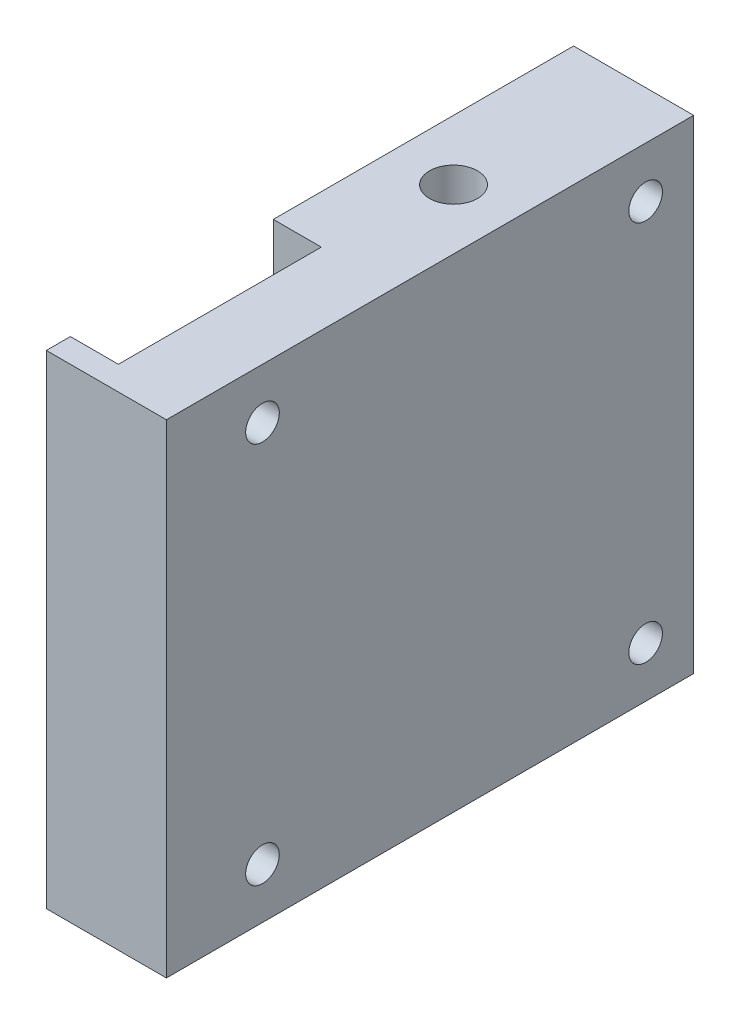
SolidWorks part; units mm, degrees
ref_plane "Front Plane" through (0, 0, 0) normal (0, 0, 1) x (1, 0, 0)
ref_plane "Top Plane" through (0, 0, 0) normal (0, 1, 0) x (1, 0, 0)
ref_plane "Right Plane" through (0, 0, 0) normal (1, 0, 0) x (0, 0, -1)
sketch "Sketch2" plane through (34.4736, 0, 0) normal (-1, 0, 0) x (0, 0, 1)
  line L0 (280.9388, 336.0766) -> (282.5512, 320.4454) construction
  line L1 (301.6995, 347.1848) -> (301.6995, 307.6848) construction
  line L2 (261.7905, 348.3924) -> (301.6995, 348.3924)
  line L3 (261.7905, 348.3924) -> (261.7905, 308.1295)
  line L4 (261.7905, 308.1295) -> (301.6995, 308.1295)
  line L5 (301.6995, 348.3924) -> (301.6995, 308.1295)
  line L6 (261.7905, 348.3924) -> (301.6995, 308.1295) construction
  line L7 (261.7905, 308.1295) -> (301.6995, 348.3924) construction
  line L8 (295.1, 308.1295) -> (299.7929, 308.1295) construction
  line L9 (297.6995, 345.5848) -> (297.6995, 342.7848) construction
  line L10 (261.7905, 328.261) -> (301.6995, 328.261) construction
  line L11 (281.745, 348.3924) -> (281.745, 308.1295) construction
  circle A0 centre (281.765, 328.1193) radius 8 construction
  circle A2 centre (297.6995, 344.1848) radius 1.4 construction
  circle A3 centre (297.6995, 344.1848) radius 1.4
  circle A4 centre (297.6995, 312.3371) radius 1.4
  circle A5 centre (265.7905, 312.3371) radius 1.4
  circle A6 centre (265.7905, 344.1848) radius 1.4
  point P4 (281.745, 328.261)
  point P5 (281.745, 328.261)
  point P19 (297.6995, 344.1848)
  point P24 (281.745, 348.3924)
  dimension "D2" = 2.8
  dimension "D1" = 40.2629
extrude "Boss-Extrude1" add sketch "Sketch2" along normal blind 10
sketch "Sketch5" plane through (24.4736, 0, 0) normal (-1, 0, 0) x (0, 0, 1)
  line L0 (297.6995, 344.6649) -> (297.6995, 343.4848) construction
  line L1 (264.4344, 311.9894) -> (267.1466, 312.6848) construction
  line L2 (265.0495, 312.6848) -> (275.5245, 312.6848) construction
  line L3 (264.3905, 344.1848) -> (267.1905, 344.1848) construction
  circle A0 centre (297.6995, 344.0749) radius 3
  circle A2 centre (265.7905, 312.3371) radius 1.4 construction
  circle A3 centre (265.7905, 312.3371) radius 3
  circle A4 centre (297.6995, 312.3371) radius 3
  circle A5 centre (265.7905, 344.1848) radius 1.4 construction
  circle A6 centre (265.7905, 344.1848) radius 3
  dimension "D1" = 6
  dimension "D2" = 6
  dimension "D3" = 6
  dimension "D4" = 6
extrude "Cut-Extrude1" cut sketch "Sketch5" against normal blind 4
sketch "Sketch6" plane through (24.4736, 0, 0) normal (-1, 0, 0) x (0, 0, 1)
  line L2 (301.6995, 348.3924) -> (261.7905, 348.3924) construction
  line L7 (286.7995, 348.3924) -> (301.6995, 348.3924)
  line L8 (286.7995, 348.3924) -> (286.7995, 318.3924)
  line L9 (286.7995, 318.3924) -> (301.6995, 318.3924)
  line L10 (301.6995, 348.3924) -> (301.6995, 318.3924)
  line L11 (286.7995, 348.3924) -> (301.6995, 318.3924) construction
  line L12 (286.7995, 318.3924) -> (301.6995, 348.3924) construction
  line L13 (301.6995, 308.1295) -> (301.6995, 348.3924) construction
  point P6 (294.2495, 333.3924)
  dimension "D5" = 30
  dimension "D6" = 14.9
extrude "Cut-Extrude2" cut sketch "Sketch6" against normal up to surface (4 mm away) up to face at (28.4736, 344.1848, 299.0995)
sketch "Sketch9" plane through (0, 0, 301.6995) normal (0, 0, 1) x (1, 0, 0)
  line L1 (24.4736, 308.1295) -> (34.4736, 308.1295)
  line L2 (24.4736, 308.1295) -> (24.4736, 348.3924)
  line L3 (24.4736, 348.3924) -> (34.4736, 348.3924)
  line L4 (34.4736, 308.1295) -> (34.4736, 348.3924)
extrude "Boss-Extrude3" add sketch "Sketch9" along normal blind 4
sketch "Sketch10" plane through (24.4736, 0, 0) normal (-1, 0, 0) x (0, 0, 1)
  line L0 (305.6995, 348.3924) -> (301.6995, 348.3924) construction
  line L1 (303.6995, 348.3924) -> (301.6995, 348.3924)
  line L2 (303.6995, 348.3924) -> (303.6995, 318.3924)
  line L3 (303.6995, 318.3924) -> (301.6995, 318.3924)
  line L4 (301.6995, 348.3924) -> (301.6995, 318.3924)
  line L5 (301.6995, 348.3924) -> (301.6995, 318.3924) construction
  line L7 (286.7995, 318.3924) -> (301.6995, 318.3924) construction
  dimension "D1" = 2
extrude "Cut-Extrude4" cut sketch "Sketch10" against normal blind 4
sketch "Sketch11" plane through (0, 348.3924, 0) normal (0, 1, 0) x (1, 0, 0)
  line L0 (24.4736, -261.7905) -> (34.4736, -261.7905) construction
  line L1 (34.4736, -305.6995) -> (34.4736, -261.7905) construction
  circle A0 centre (29.4736, -276.7905) radius 2
  dimension "D1" = 4
  dimension "D2" = 15
  dimension "D3" = 5
extrude "Cut-Extrude5" cut sketch "Sketch11" against normal blind 6
